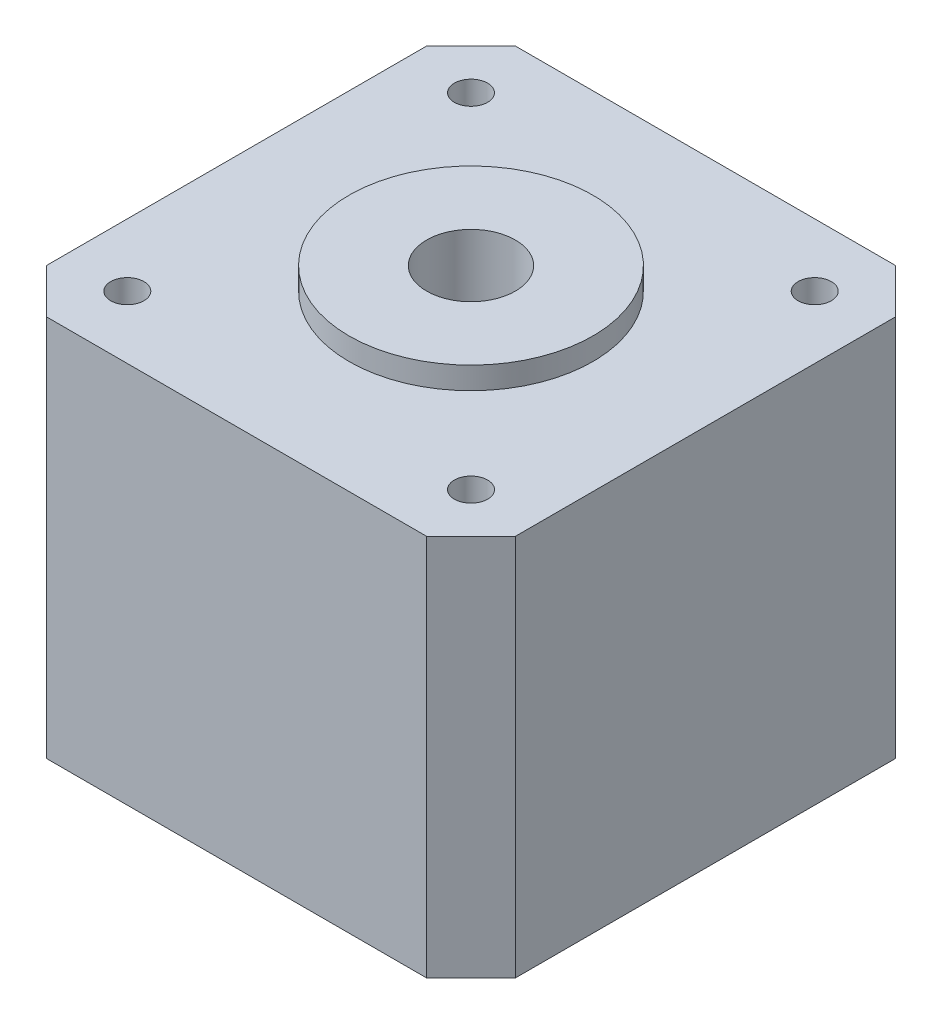
SolidWorks part; units mm, degrees
ref_plane "前视基准面" through (0, 0, 0) normal (0, 0, 1) x (1, 0, 0)
ref_plane "上视基准面" through (0, 0, 0) normal (0, 1, 0) x (1, 0, 0)
ref_plane "右视基准面" through (0, 0, 0) normal (1, 0, 0) x (0, 0, -1)
sketch "草图1" plane through (0, 0, 0) normal (0, 1, 0) x (1, 0, 0)
  line L1 (-21.15, 21.15) -> (21.15, 21.15)
  line L2 (-21.15, 21.15) -> (-21.15, -21.15)
  line L3 (-21.15, -21.15) -> (21.15, -21.15)
  line L4 (21.15, 21.15) -> (21.15, -21.15)
  line L5 (-21.15, 21.15) -> (21.15, -21.15) construction
  line L6 (-21.15, -21.15) -> (21.15, 21.15) construction
  point P0 (0, 0)
  dimension "D1" = 42.3
  dimension "D2" = 42.3
extrude "凸台-拉伸1" add sketch "草图1" along normal blind 34.5
sketch "草图2" plane through (0, 34.5, 0) normal (0, 1, 0) x (1, 0, 0)
  circle A0 centre (0, 0) radius 11
  dimension "D1" = 22
extrude "凸台-拉伸2" add sketch "草图2" along normal blind 2
sketch "草图3" plane through (0, 34.5, 0) normal (0, 1, 0) x (1, 0, 0)
  line L0 (0, 0) -> (0, 22.1405) construction
  line L1 (0, 0) -> (27.2651, 0) construction
  circle A0 centre (-15.5, 15.5) radius 1.5
  circle A1 centre (15.5, 15.5) radius 1.5
  circle A2 centre (15.5, -15.5) radius 1.5
  circle A3 centre (-15.5, -15.5) radius 1.5
  dimension "D1" = 3
  dimension "D2" = 31
  dimension "D3" = 31
extrude "切除-拉伸1" cut sketch "草图3" against normal blind 5
sketch "草图4" plane through (0, 36.5, 0) normal (0, 1, 0) x (1, 0, 0)
  circle A0 centre (0, 0) radius 4
  dimension "D1" = 8
extrude "切除-拉伸2" cut sketch "草图4" against normal through all
chamfer "倒角1" distance 4 angle 45 4 edges at (21.15, 17.25, -21.15) (21.15, 17.25, 21.15) (-21.15, 17.25, 21.15) (-21.15, 17.25, -21.15)
